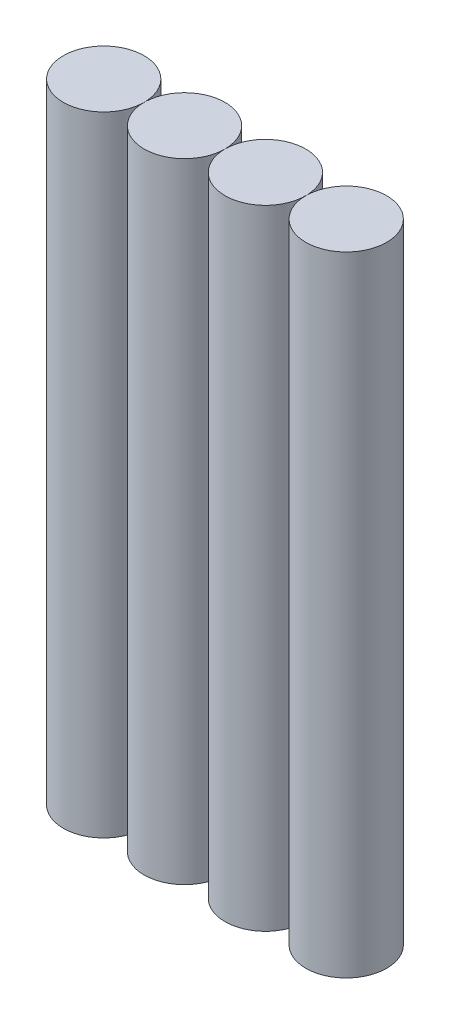
SolidWorks part; units mm, degrees
ref_plane "Front Plane" through (0, 0, 0) normal (0, 0, 1) x (1, 0, 0)
ref_plane "Top Plane" through (0, 0, 0) normal (0, 1, 0) x (1, 0, 0)
ref_plane "Right Plane" through (0, 0, 0) normal (1, 0, 0) x (0, 0, -1)
sketch "Sketch1" plane through (0, 0, 0) normal (0, 1, 0) x (1, 0, 0)
  line L0 (0, 0) -> (54, 0) construction
  circle A0 centre (0, 0) radius 9
  circle A1 centre (18, 0) radius 9
  circle A2 centre (36, 0) radius 9
  circle A3 centre (54, 0) radius 9
  dimension "D1" = 18
extrude "Boss-Extrude1" add sketch "Sketch1" along normal blind 140
